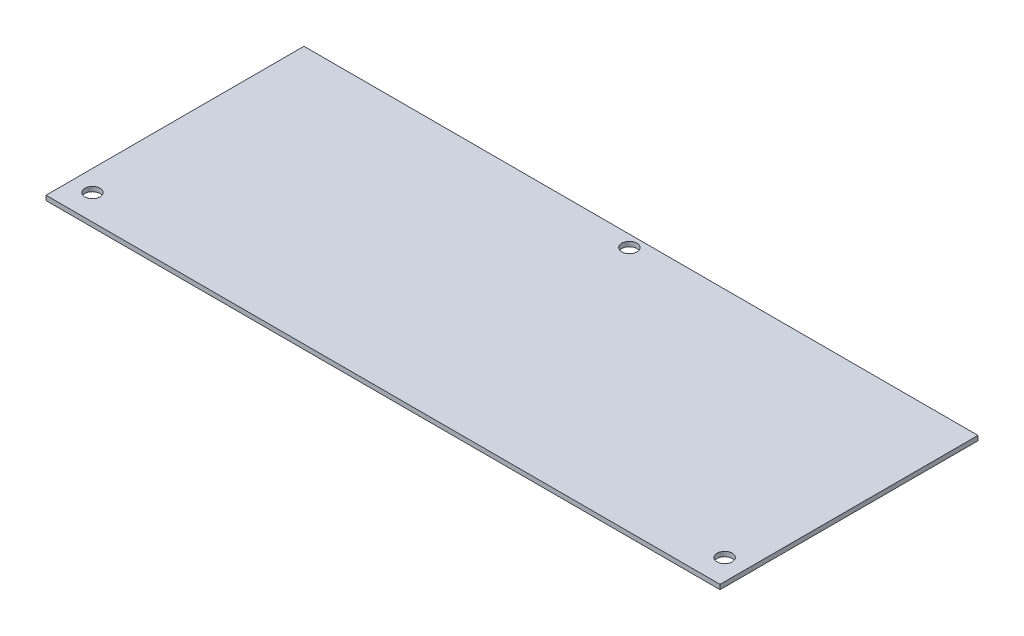
SolidWorks part; units mm, degrees
ref_plane "Front Plane" through (0, 0, 0) normal (0, 0, 1) x (1, 0, 0)
ref_plane "Top Plane" through (0, 0, 0) normal (0, 1, 0) x (1, 0, 0)
ref_plane "Right Plane" through (0, 0, 0) normal (1, 0, 0) x (0, 0, -1)
sketch "Sketch2" plane through (0, 0, 0) normal (0, 1, 0) x (1, 0, 0)
  line L1 (0, 0) -> (-290, 0)
  line L2 (0, 0) -> (0, -111)
  line L3 (0, -111) -> (-290, -111)
  line L4 (-290, 0) -> (-290, -111)
  circle A0 centre (-145, -5) radius 3.25
  circle A1 centre (-281, -100) radius 3.25
  circle A2 centre (-9, -100) radius 3.25
  dimension "D3" = 6.5
  dimension "D4" = 9
  dimension "D6" = 6.5
  dimension "D7" = 9
  dimension "D8" = 11
  dimension "D9" = 6.5
  dimension "D10" = 5
  dimension "D11" = 145
  dimension "D1" = 290
  dimension "D2" = 111
  dimension "D5" = 11
extrude "Boss-Extrude1" add sketch "Sketch2" along normal blind 2
